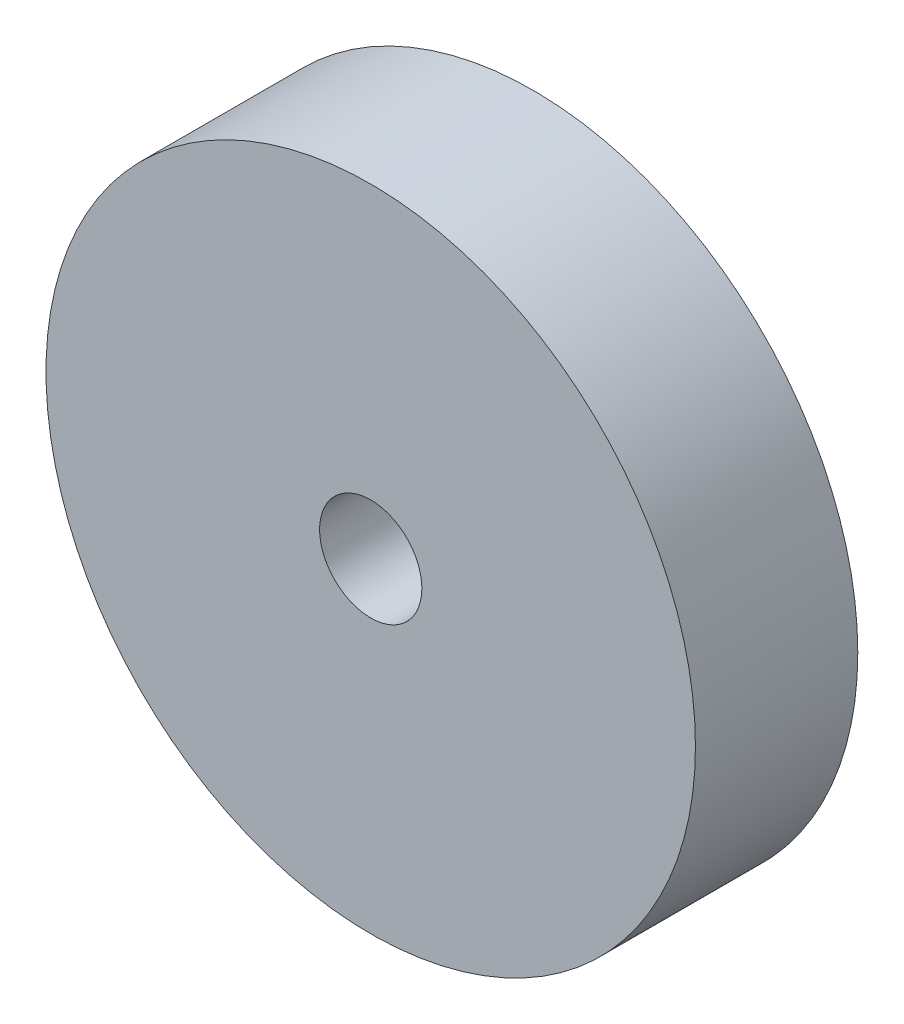
SolidWorks part; units mm, degrees
ref_plane "Front Plane" through (0, 0, 0) normal (0, 0, 1) x (1, 0, 0)
ref_plane "Top Plane" through (0, 0, 0) normal (0, 1, 0) x (1, 0, 0)
ref_plane "Right Plane" through (0, 0, 0) normal (1, 0, 0) x (0, 0, -1)
sketch "Sketch1" plane through (0, 0, 0) normal (0, 0, 1) x (1, 0, 0)
  circle A0 centre (0, 0) radius 25.4
  circle A1 centre (0, 0) radius 4
extrude "Boss-Extrude1" add sketch "Sketch1" along normal blind 12.7
